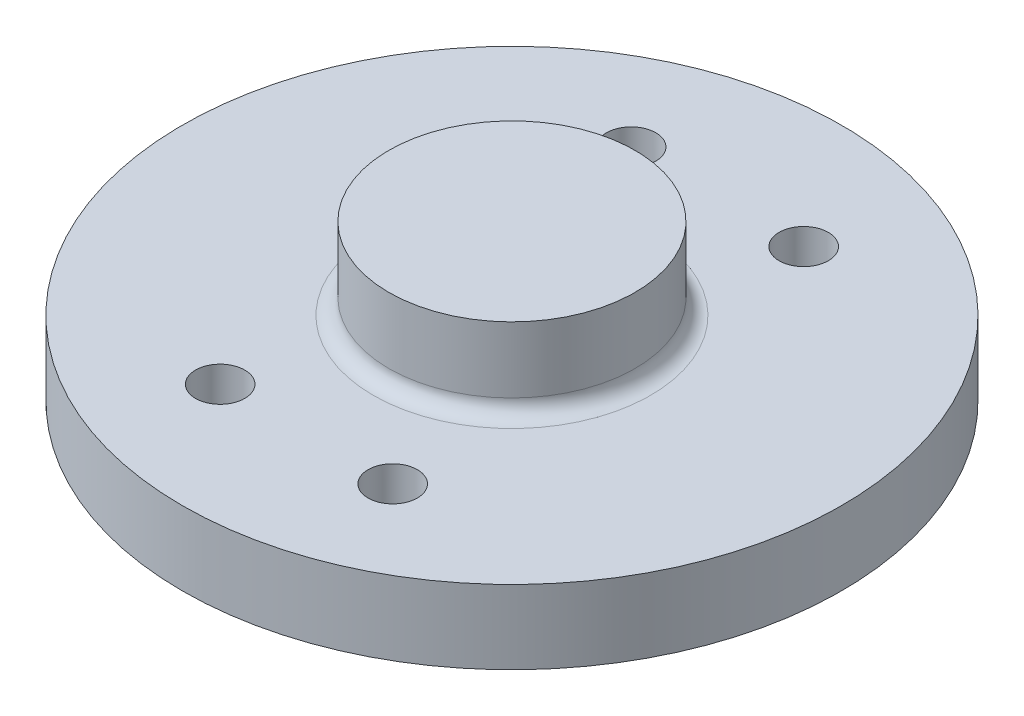
SolidWorks part; units mm, degrees
ref_plane "Alzado" through (0, 0, 0) normal (0, 0, 1) x (1, 0, 0)
ref_plane "Planta" through (0, 0, 0) normal (0, 1, 0) x (1, 0, 0)
ref_plane "Vista lateral" through (0, 0, 0) normal (1, 0, 0) x (0, 0, -1)
sketch "Croquis1" plane through (0, 0, 0) normal (0, 1, 0) x (1, 0, 0)
  circle A0 centre (0, 0) radius 85
  dimension "D1" = 170
extrude "Saliente-Extruir1" add sketch "Croquis1" along normal blind 19.05
sketch "Croquis2" plane through (0, 19.05, 0) normal (0, 1, 0) x (1, 0, 0)
  circle A0 centre (0, 0) radius 31.75
  dimension "D1" = 63.5
extrude "Saliente-Extruir2" add sketch "Croquis2" along normal blind 21
fillet "Redondeo1" radius 4 1 edges at (0, 19.05, 31.75)
sketch "Croquis3" plane through (0, 19.05, 0) normal (0, 1, 0) x (1, 0, 0)
  line L0 (-85, 0) -> (85, 0) construction
  line L1 (0, -85) -> (0, 85) construction
  circle A0 centre (0, 0) radius 85 construction
  circle A1 centre (-22.25, -53) radius 6.35
  circle A2 centre (-22.25, 53) radius 6.35
  circle A3 centre (22.25, 53) radius 6.35
  circle A4 centre (22.25, -53) radius 6.35
  dimension "D1" = 12.7
  dimension "D2" = 53
  dimension "D3" = 22.25
extrude "Cortar-Extruir1" cut sketch "Croquis3" against normal up to surface (19.05 mm away) up to face at (0, 0, 85)
